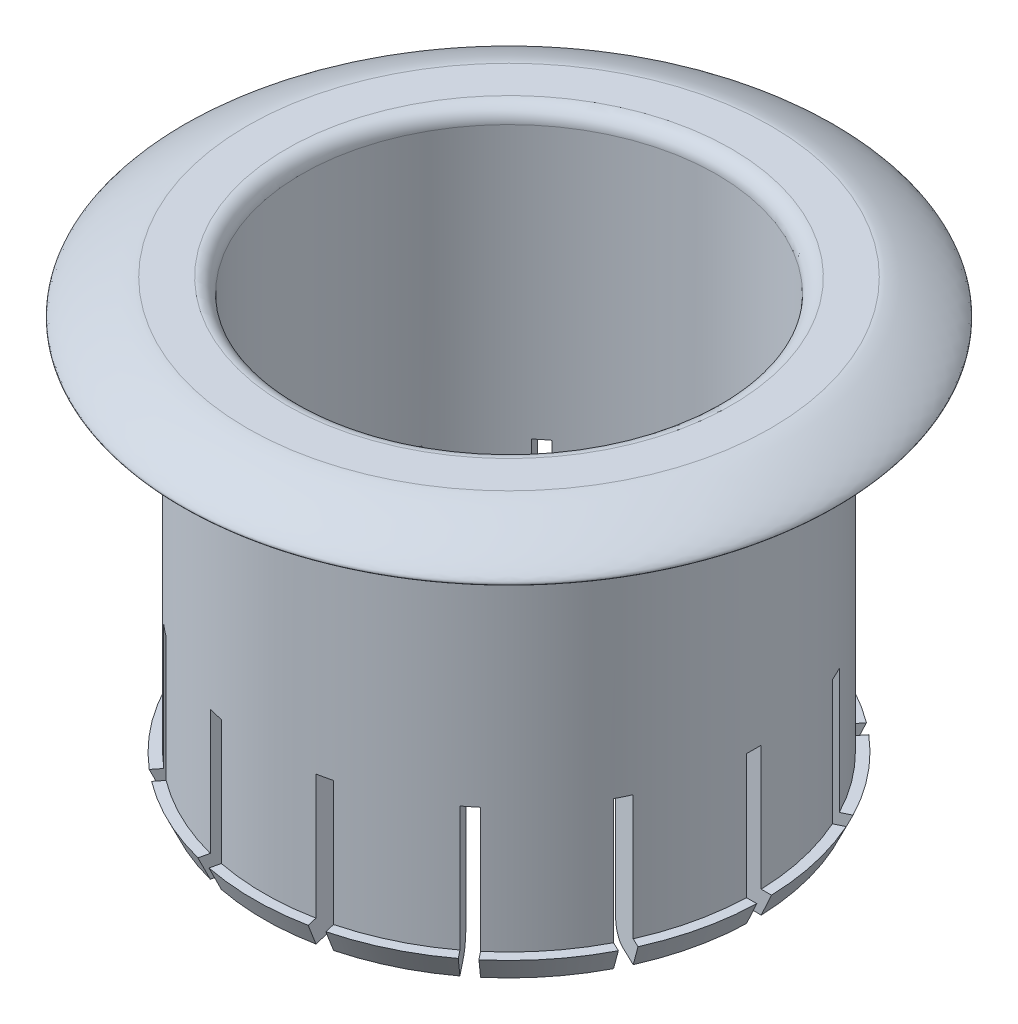
SolidWorks part; units mm, degrees
material "ABS"
ref_plane "Front Plane" through (0, 0, 0) normal (0, 0, 1) x (1, 0, 0)
ref_plane "Top Plane" through (0, 0, 0) normal (0, 1, 0) x (1, 0, 0)
ref_plane "Right Plane" through (0, 0, 0) normal (1, 0, 0) x (0, 0, -1)
sketch "Sketch1" plane through (0, 0, 0) normal (0, 0, 1) x (1, 0, 0)
  line L0 (0, 0) -> (14.097, 0) construction
  line L1 (14.097, 0) -> (16.637, 0)
  line L2 (16.637, 0) -> (16.637, 26.924)
  line L3 (16.637, 26.924) -> (21.717, 26.924)
  line L4 (14.097, 0) -> (14.097, 29.464)
  line L5 (14.097, 29.464) -> (17.7844, 29.464)
  line L6 (19.1269, 29.464) -> (16.4199, 29.464) construction
  line L7 (18.6537, 26.924) -> (21.9509, 26.924) construction
  line L8 (0, 0) -> (0, 29.464) construction
  line L9 (0, 29.464) -> (14.097, 29.464) construction
  line L10 (16.637, 1.524) -> (17.337, 1.524)
  line L11 (17.337, 1.524) -> (16.637, 0)
  spline S0 degree 3 poles (17.7844, 29.464) (18.9123, 29.464) (23.7777, 26.924) (21.717, 26.924) knots 0 0 0 0 1 1 1 1
  dimension "D1" = 16.637
  dimension "D2" = 2.54
  dimension "D3" = 2.54
  dimension "D4" = 26.924
  dimension "D5" = 5.08
  dimension "D6" = 25.4
  dimension "D7" = 0.7
revolve "Revolve1" add sketch "Sketch1" angle 360 about L8
fillet "Fillet1" radius 1 2 edges at (0, 0, -14.097) (0, 29.464, -14.097)
sketch "Sketch2" plane through (0, 0, 0) normal (0, 0, 1) x (1, 0, 0)
  line L0 (-16.637, 0) -> (16.637, 0) construction
  line L1 (-17.337, 0) -> (17.337, 0)
  line L2 (-17.337, 0) -> (-17.337, 10)
  line L3 (-17.337, 10) -> (17.337, 10)
  line L4 (17.337, 0) -> (17.337, 10)
  point P4 (-17.7611, 3.5033)
  point P5 (-15.758, 0)
  point P8 (-17.7654, 3)
  dimension "D1" = 10
extrude "Cut-Extrude1" cut sketch "Sketch2" against normal mid plane 1
pattern_circular "CirPattern1" count 7 over 360 about axis through (0, 0, 0) along (0, 1, 0) of "Cut-Extrude1"
